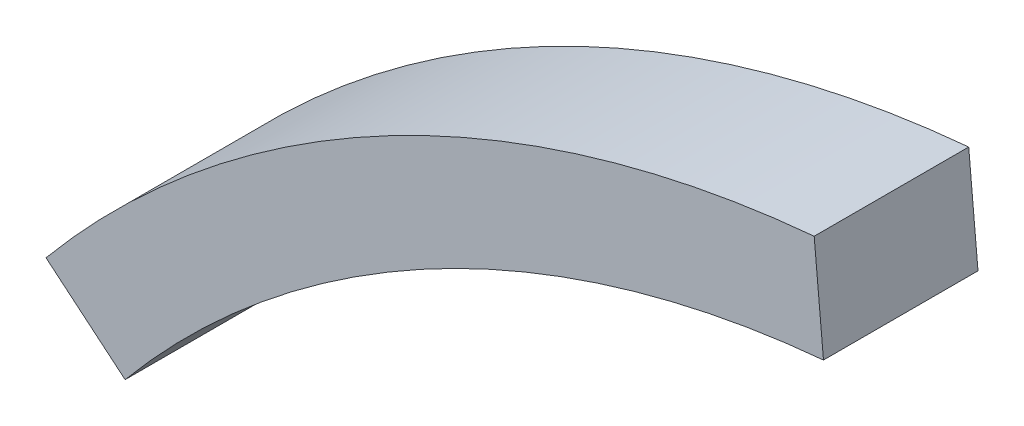
SolidWorks part; units mm, degrees
ref_plane "Front Plane" through (0, 0, 0) normal (0, 0, 1) x (1, 0, 0)
ref_plane "Top Plane" through (0, 0, 0) normal (0, 1, 0) x (1, 0, 0)
ref_plane "Right Plane" through (0, 0, 0) normal (1, 0, 0) x (0, 0, -1)
sketch "Sketch1" plane through (0, 0, 0) normal (0, 0, 1) x (1, 0, 0)
  line L0 (-15.3585, 12.8108) -> (-16.8943, 14.0919)
  line L1 (-1.8014, 19.9187) -> (-1.9816, 21.9106)
  arc A0 (-1.9816, 21.9106) -> (-16.8943, 14.0919) centre (0, 0) ccw
  arc A1 (-1.8014, 19.9187) -> (-15.3585, 12.8108) centre (0, 0) ccw
  dimension "D1" = 44
  dimension "D2" = 40
extrude "Boss-Extrude1" add sketch "Sketch1" along normal blind 3
